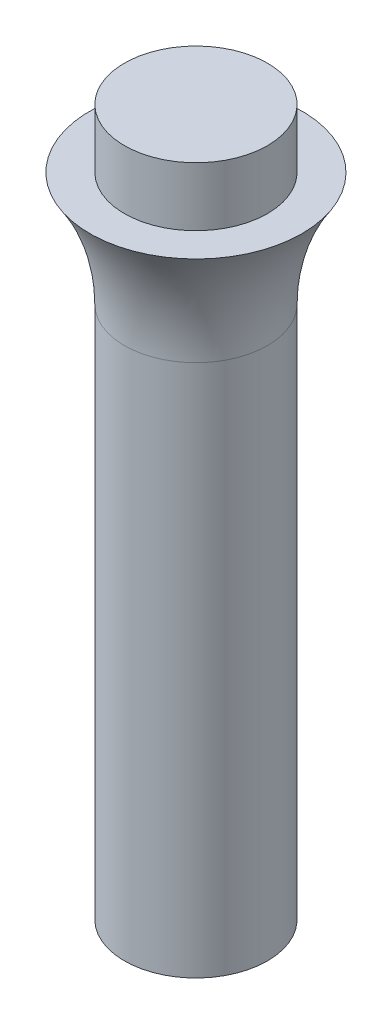
SolidWorks part; units mm, degrees
ref_plane "Alzado" through (0, 0, 0) normal (0, 0, 1) x (1, 0, 0)
ref_plane "Planta" through (0, 0, 0) normal (0, 1, 0) x (1, 0, 0)
ref_plane "Vista lateral" through (0, 0, 0) normal (1, 0, 0) x (0, 0, -1)
sketch "Croquis1" plane through (0, 0, 0) normal (0, 0, 1) x (1, 0, 0)
  line L0 (3.8287, 31.9057) -> (0.7287, 31.9057)
  line L1 (0.7287, 31.9057) -> (0.7287, 15.2973)
  line L2 (0.7287, 15.2973) -> (1.9787, 15.2973)
  line L3 (1.9787, 15.2973) -> (1.9787, 1.2973)
  line L4 (1.9787, 1.2973) -> (3.8287, 1.2973)
  line L5 (3.8287, 1.2973) -> (3.8287, 24.3984)
  line L6 (5.3287, 29.3532) -> (3.8287, 29.3532)
  line L7 (3.8287, 29.3532) -> (3.8287, 31.9057)
  line L8 (0.7287, 31.9057) -> (0.7287, 0) construction
  arc A0 (3.8287, 24.3984) -> (5.3287, 29.3532) centre (12.7623, 24.3984) cw
  point P11 (3.8287, 30.6295)
  point P12 (1.9787, 8.2973)
  dimension "D1" = 23.101
  dimension "D2" = 3.1
  dimension "D3" = 1.25
  dimension "D4" = 1.5
  dimension "D5" = 14
revolve "Revolución1" add sketch "Croquis1" angle 360 about L8
